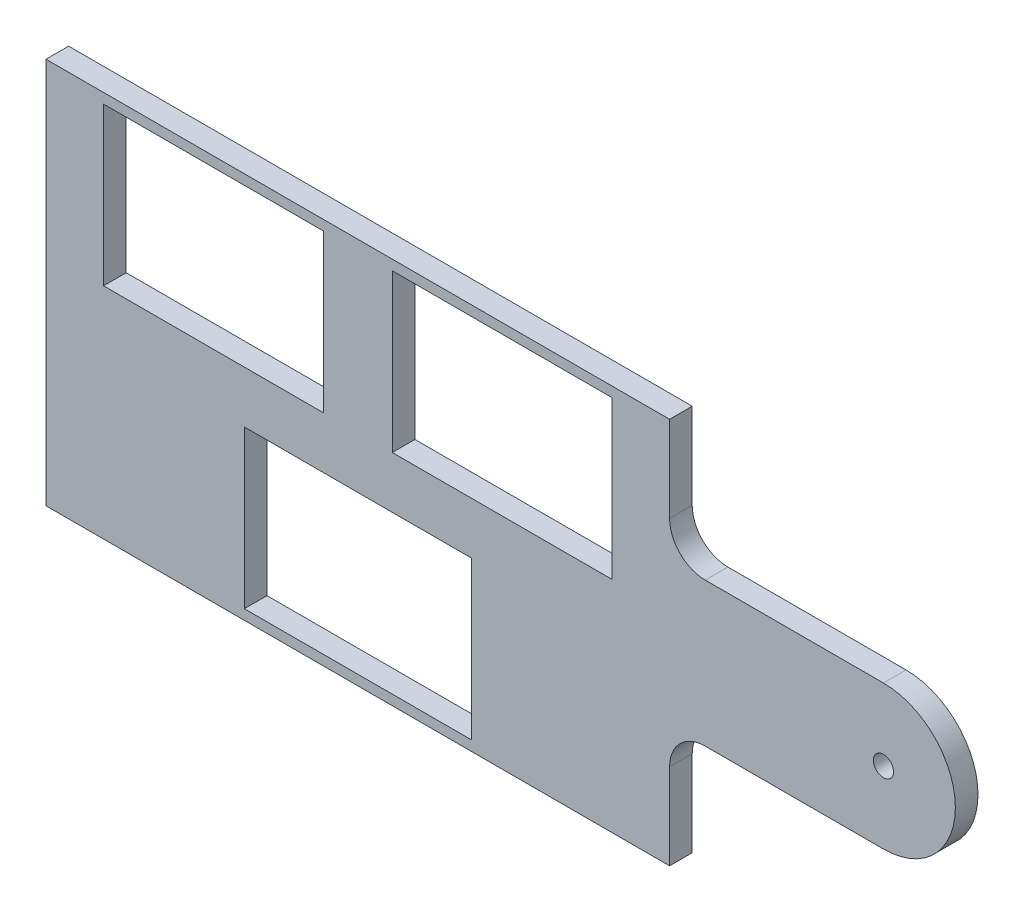
SolidWorks part; units mm, degrees
other "Markup1"
sketch "Sketch7" plane through (-43.735, -27.035, 3.175) normal (0, 0, 1) x (1, 0, 0)
material "Maple"
ref_plane "Front Plane" through (0, 0, 0) normal (0, 0, 1) x (1, 0, 0)
ref_plane "Top Plane" through (0, 0, 0) normal (0, 1, 0) x (1, 0, 0)
ref_plane "Right Plane" through (0, 0, 0) normal (1, 0, 0) x (0, 0, -1)
sketch "Sketch1" plane through (0, 0, 0) normal (0, 0, 1) x (1, 0, 0)
  line L1 (-43.735, 30.3) -> (43.735, 30.3)
  line L2 (-43.735, 30.3) -> (-43.735, -30.3)
  line L3 (-43.735, -30.3) -> (43.735, -30.3)
  line L4 (43.735, 30.3) -> (43.735, -30.3)
  line L5 (-43.735, 30.3) -> (43.735, -30.3) construction
  line L6 (-43.735, -30.3) -> (43.735, 30.3) construction
  point P0 (0, 0)
  dimension "D1" = 87.47
  dimension "D2" = 60.6
extrude "Boss-Extrude1" add sketch "Sketch1" along normal blind 3.175
sketch "Sketch2" plane through (0, 0, 3.175) normal (0, 0, 1) x (1, 0, 0)
  line L0 (0, 0) -> (-25, 0) construction
  line L5 (-25, 0) -> (-25, -26.8) construction
  line L6 (0, 0) -> (0, -25.8) construction
  line L7 (16, -3.55) -> (-16, -3.55)
  line L8 (-16, -3.55) -> (-16, -25.8)
  line L9 (-16, -25.8) -> (16, -25.8)
  line L10 (16, -3.55) -> (16, -25.8)
  line L11 (0, 0) -> (0, 25.8) construction
  line L13 (0, 3.55) -> (-24.5, 3.55) construction
  line L18 (-20.25, 3.55) -> (-20.25, 14.675) construction
  line L19 (35.75, 3.55) -> (4.75, 3.55)
  line L23 (-35.75, 25.8) -> (-4.75, 25.8)
  line L24 (-35.75, 25.8) -> (-35.75, 3.55)
  line L25 (-35.75, 3.55) -> (-4.75, 3.55)
  line L26 (-4.75, 25.8) -> (-4.75, 3.55)
  line L27 (-35.75, 25.8) -> (-4.75, 3.55) construction
  line L28 (-35.75, 3.55) -> (-4.75, 25.8) construction
  line L29 (4.75, 25.8) -> (4.75, 3.55)
  line L30 (35.75, 25.8) -> (4.75, 25.8)
  line L31 (35.75, 25.8) -> (35.75, 3.55)
  line L32 (35.665, 3.635) -> (4.835, 3.635)
  line L33 (16, -14.675) -> (0, -14.675) construction
  line L34 (-43.735, -30.3) -> (43.735, -30.3) construction
  line L35 (4.835, 25.715) -> (4.835, 3.635)
  line L36 (35.665, 25.715) -> (4.835, 25.715)
  line L37 (35.665, 25.715) -> (35.665, 3.635)
  line L38 (-35.665, 25.715) -> (-35.665, 3.635)
  line L39 (-35.665, 3.635) -> (-4.835, 3.635)
  line L40 (-4.835, 25.715) -> (-4.835, 3.635)
  line L41 (-35.665, 25.715) -> (-4.835, 25.715)
  line L42 (-15.915, -25.715) -> (15.915, -25.715)
  line L43 (15.915, -3.635) -> (15.915, -25.715)
  line L44 (15.915, -3.635) -> (-15.915, -3.635)
  line L45 (-15.915, -3.635) -> (-15.915, -25.715)
  point P0 (0, 0)
  point P3 (0, -3.55)
  point P7 (0, 3.55)
  point P12 (0, -3.55)
  point P14 (-16, 3.55)
  point P17 (0, 14.93)
  point P18 (-20.25, 3.55)
  point P35 (20.25, 3.55)
  dimension "D2" = 26.8
  dimension "D4" = 16
  dimension "D6" = 24.5
  dimension "D7" = 22.25
  dimension "D8" = 8.5
  dimension "D11" = 4.25
  dimension "D12" = 31
  dimension "D13" = 22.25
  dimension "D3" = 4.5
  dimension "D9" = 7.1
  dimension "D5" = 3.55
  dimension "D10" = 11.38
  dimension "D14" = 0.085
  dimension "D15" = 0.085
  dimension "D16" = 0.085
sketch "Sketch3" plane through (0, 0, 3.175) normal (0, 0, 1) x (1, 0, 0)
  line L0 (43.735, -30.3) -> (43.735, 30.3) construction
  line L2 (43.735, 10.085) -> (43.735, -10.085)
  line L3 (43.735, 10.085) -> (73.735, 10.085)
  line L4 (43.735, -10.085) -> (73.735, -10.085)
  arc A0 (73.735, 10.085) -> (73.735, -10.085) centre (73.735, 0) cw
  point P5 (43.735, 0)
  dimension "D1" = 20.17
  dimension "D2" = 30
extrude "Boss-Extrude2" add sketch "Sketch3" against normal blind 3.175
fillet "Fillet1" radius 5 2 edges at (43.735, -10.085, 1.5875) (43.735, 10.085, 1.5875)
sketch "Sketch5" plane through (0, 0, 3.175) normal (0, 0, 1) x (1, 0, 0)
  line L0 (83.82, 0) -> (73.735, 0) construction
  arc A0 (73.735, -10.085) -> (73.735, 10.085) centre (73.735, 0) ccw construction
  circle A1 centre (73.735, 0) radius 1.415
  dimension "D1" = 2.83
extrude "Cut-Extrude2" cut sketch "Sketch5" against normal blind 10
sketch "Sketch6" plane through (0, 0, 3.175) normal (0, 0, 1) x (1, 0, 0)
  line L0 (0, 0) -> (-43.735, 0) construction
  line L1 (-43.735, 30.3) -> (-43.735, -30.3) construction
  line L2 (-43.735, 0) -> (-43.735, 27.035) construction
  line L3 (-43.735, 0) -> (-43.735, -27.035) construction
  line L4 (-43.735, 27.035) -> (43.735, 27.035)
  line L5 (43.735, 15.085) -> (43.735, 30.3) construction
  line L6 (43.735, 27.035) -> (43.735, 30.3)
  line L7 (43.735, 30.3) -> (-43.735, 30.3)
  line L8 (-43.735, 30.3) -> (-43.735, 27.035)
  line L9 (43.735, -30.3) -> (-43.735, -30.3)
  line L10 (43.735, -27.035) -> (43.735, -30.3)
  line L11 (-43.735, -27.035) -> (43.735, -27.035)
  line L12 (-43.735, -30.3) -> (-43.735, -27.035)
  dimension "D1" = 27.035
extrude "Cut-Extrude3" cut sketch "Sketch6" against normal blind 10
extrude "Cut-Extrude4" cut sketch "Sketch2" against normal blind 10 contours L38 L39 L40 L41 | L32 L35 L36 L37 | L42 L43 L44 L45
sketch "Sketch8" plane through (0, 0, 3.175) normal (0, 0, 1) x (1, 0, 0)
  line L0 (-43.735, 27.035) -> (-43.735, 27.125)
  line L1 (-43.735, 27.125) -> (43.735, 27.125)
  line L2 (43.735, 27.125) -> (43.735, 27.035)
  line L3 (43.735, 27.035) -> (-43.735, 27.035)
  line L4 (-43.735, -27.035) -> (43.735, -27.035)
  line L5 (43.735, -27.035) -> (43.735, -27.125)
  line L6 (43.735, -27.125) -> (-43.735, -27.125)
  line L7 (-43.735, -27.125) -> (-43.735, -27.035)
  dimension "D1" = 0.09
  dimension "D2" = 0.09
extrude "Boss-Extrude3" add sketch "Sketch8" against normal blind 3.175
equation "\"length\"=90"
equation "\"dist2\"=87.3"
equation "\"D1@Sketch1\"=\"dist2\" + 2*\"kerf\""
equation "\"width\"=69.1446"
equation "\"depth\"= 6.35"
equation "\"length2\"= 40.00mm"
equation "\"kerf\"= 0.17 / 2"
equation "\"D7@Sketch2\"=22.25mm "
equation "\"D13@Sketch2\"=22.25mm "
equation "\"D12@Sketch2\"=31.00mm"
equation "\"D4@Sketch2\"=16.00mm"
equation "\"D1@Sketch6\"= 26.95mm + \"kerf\""
equation "\"D1@Sketch3\"= 20.00mm + 2*\"kerf\""
